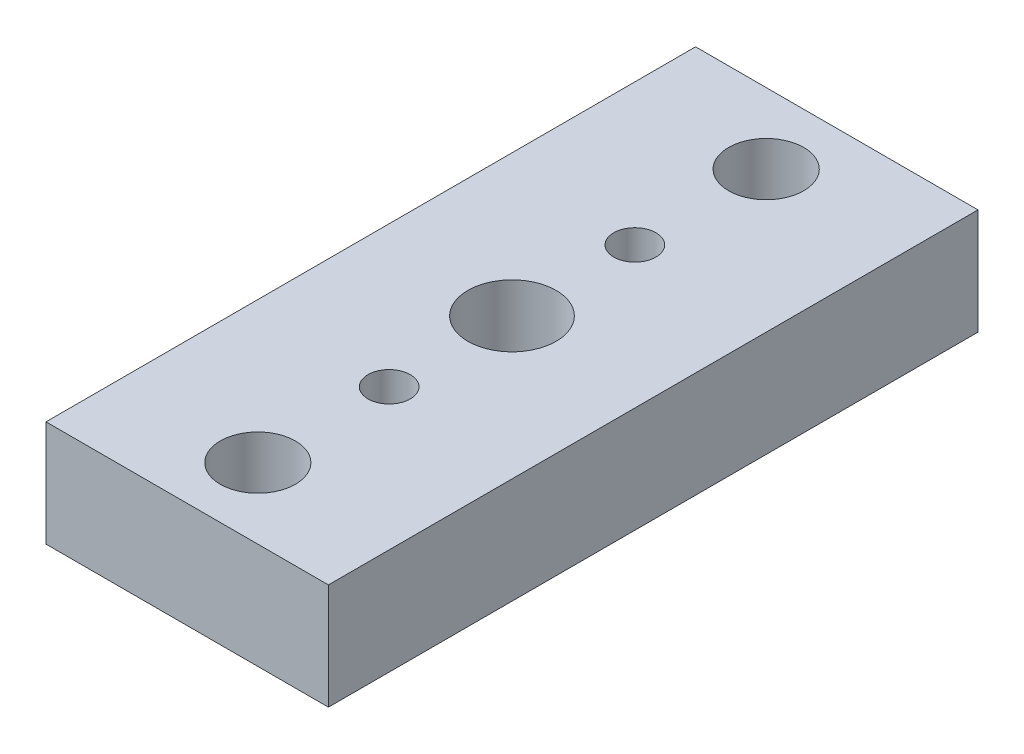
SolidWorks part; units mm, degrees
material "6061-T6 (SS)"
ref_plane "Front Plane" through (0, 0, 0) normal (0, 0, 1) x (1, 0, 0)
ref_plane "Top Plane" through (0, 0, 0) normal (0, 1, 0) x (1, 0, 0)
ref_plane "Right Plane" through (0, 0, 0) normal (1, 0, 0) x (0, 0, -1)
sketch "Sketch1" plane through (0, 0, 0) normal (0, 0, 1) x (1, 0, 0)
  line L0 (-12.7, -4.7625) -> (12.7, -4.7625)
  line L1 (-12.7, -4.7625) -> (-12.7, 4.7625)
  line L2 (12.7, -4.7625) -> (12.7, 4.7625)
  line L3 (-12.7, 4.7625) -> (12.7, 4.7625)
  line L4 (-12.7, -4.7625) -> (12.7, 4.7625) construction
  line L5 (12.7, -4.7625) -> (-12.7, 4.7625) construction
  point P1 (0, 0)
extrude "Extrude1" add sketch "Sketch1" along normal blind 58.42
sketch "Sketch2" plane through (0, 4.7625, 0) normal (0, 1, 0) x (1, 0, 0)
  line L0 (0, 0) -> (0, -6.35) construction
  line L1 (0, -58.42) -> (0, -52.07) construction
  line L2 (12.7, -58.42) -> (-12.7, -58.42) construction
  line L3 (-12.7, -29.21) -> (12.7, -29.21) construction
  line L4 (-12.7, -58.42) -> (-12.7, 0) construction
  line L5 (12.7, -58.42) -> (12.7, 0) construction
  line L6 (0, -29.21) -> (0, -40.259) construction
  point P13 (0, -29.21)
  dimension "D1" = 45.72
  dimension "D2" = 11.049
  dimension "D3" = 6.35
hole_wizard "1/4 Clearance Hole1" positions "3DSketch1" profile "Sketch3" hole size "1/4" standard "Ansi Inch"
sketch3d "3DSketch1"
  point P0 (0, 4.7625, 6.35)
  point P4 (0, 4.7625, 52.07)
sketch "Sketch3" plane through (0, 4.7625, 6.35) normal (1, 0, 0) x (0, 0, 1)
  line L0 (0, 0) -> (0, 14.7298)
  line L1 (0, 14.7298) -> (3.3782, 12.7)
  line L2 (3.3782, 12.7) -> (3.3782, 0)
  line L5 (3.3782, 0) -> (0, 0)
  line L10 (0, 14.7298) -> (-3.3782, 12.7) construction
  line L11 (0, -6.35) -> (0, 107.95) construction
  dimension "Hole Dia." = 6.7564
  dimension "Hole Depth" = 12.7
  dimension "Drill Angle" = 118
hole_wizard "3/8-16 Tapped Hole1" positions "3DSketch3" profile "Sketch5" tap size "3/8-16" standard "Ansi Inch" end condition through all
sketch3d "3DSketch3"
  point P0 (0, 4.7625, 29.21)
sketch "Sketch5" plane through (0, 4.7625, 29.21) normal (1, 0, 0) x (0, 0, 1)
  line L0 (0, 0) -> (0, 9.525)
  line L1 (0, 9.525) -> (3.9687, 9.525)
  line L2 (3.9687, 9.525) -> (3.9687, 0)
  line L5 (3.9687, 0) -> (0, 0)
  line L11 (0, -6.35) -> (0, 107.95) construction
  dimension "Thread Major Dia." = 7.9375
  dimension "Thru Tap Drill Depth" = 9.525
hole_wizard "#10-24 Tapped Hole1" positions "3DSketch4" profile "Sketch6" tap size "#10-24" standard "Ansi Inch" end condition through all
sketch3d "3DSketch4"
  point P0 (0, 4.7625, 40.259)
sketch "Sketch6" plane through (0, 4.7625, 40.259) normal (1, 0, 0) x (0, 0, 1)
  line L0 (0, 0) -> (0, 9.525)
  line L1 (0, 9.525) -> (1.8986, 9.525)
  line L2 (1.8986, 9.525) -> (1.8986, 0)
  line L5 (1.8986, 0) -> (0, 0)
  line L11 (0, -6.35) -> (0, 107.95) construction
  dimension "Thread Major Dia." = 3.7973
  dimension "Thru Tap Drill Depth" = 9.525
pattern_circular "CirPattern1" count 2 over 360 about axis through (0, 0, 29.21) along (0, 1, 0) of "#10-24 Tapped Hole1"
